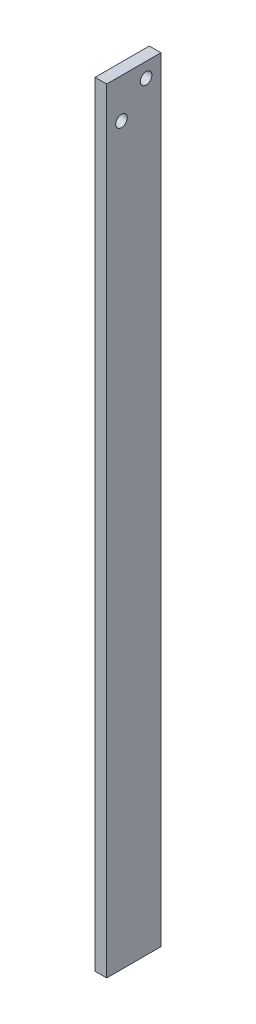
SolidWorks part; units mm, degrees
ref_plane "前视基准面" through (0, 0, 0) normal (0, 0, 1) x (1, 0, 0)
ref_plane "上视基准面" through (0, 0, 0) normal (0, 1, 0) x (1, 0, 0)
ref_plane "右视基准面" through (0, 0, 0) normal (1, 0, 0) x (0, 0, -1)
other "Configuration Table"
sketch "草图1" plane through (0, 0, 0) normal (1, 0, 0) x (0, 0, -1)
  line L0 (14, 0) -> (0, -14) construction
  line L1 (0, 0) -> (14, 0)
  line L2 (0, 0) -> (0, -200)
  line L3 (0, -200) -> (14, -200)
  line L4 (14, 0) -> (14, -200)
  line L5 (0, 0) -> (14, 0) construction
  line L6 (0, 0) -> (0, -14) construction
  line L7 (0, -14) -> (14, -14) construction
  line L8 (14, 0) -> (14, -14) construction
  circle A0 centre (7, -7) radius 4.5 construction
  circle A1 centre (10.182, -3.818) radius 1.5
  circle A2 centre (3.818, -10.182) radius 1.5
  dimension "D4" = 3
  dimension "D5" = 3
  dimension "D1" = 14
  dimension "D2" = 200
  dimension "D3" = 14
extrude "凸台-拉伸1" add sketch "草图1" along normal blind 3
